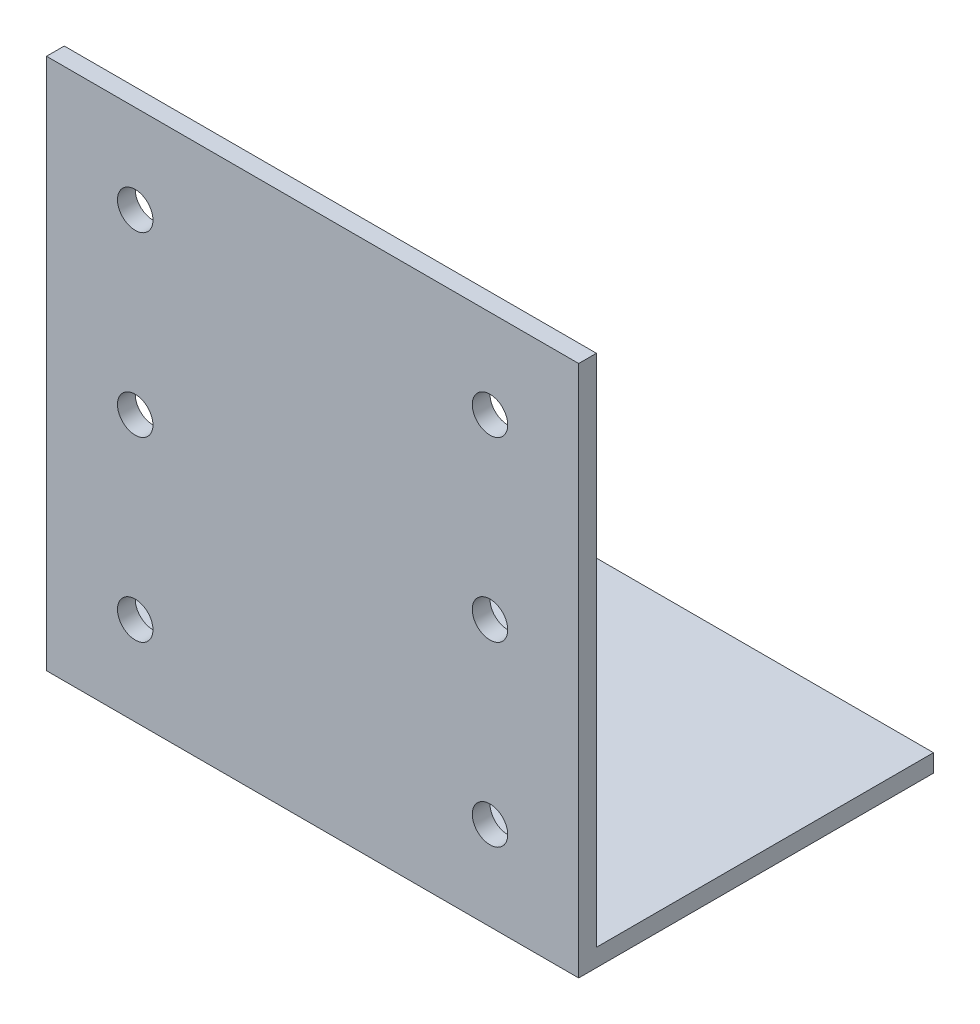
SolidWorks part; units mm, degrees
ref_plane "Спереди" through (0, 0, 0) normal (0, 0, 1) x (1, 0, 0)
ref_plane "Сверху" through (0, 0, 0) normal (0, 1, 0) x (1, 0, 0)
ref_plane "Справа" through (0, 0, 0) normal (1, 0, 0) x (0, 0, -1)
sketch "Эскиз1" plane through (0, 0, 0) normal (1, 0, 0) x (0, 0, -1)
  line L0 (0, 0) -> (0, 60)
  line L1 (0, 0) -> (40, 0)
extrude "Вытянуть-Тонкостенный1" add sketch "Эскиз1" along normal blind 60 thin
sketch "Эскиз2" plane through (0, 0, 0) normal (0, 0, 1) x (1, 0, 0)
  circle A0 centre (10, 50) radius 2
  circle A1 centre (50, 50) radius 2
  circle A2 centre (50, 30) radius 2
  circle A3 centre (50, 10) radius 2
  circle A5 centre (10, 30) radius 2
  circle A6 centre (10, 10) radius 2
  dimension "D1" = 2
  dimension "D2" = 3
extrude "Вырез-Вытянуть1" cut sketch "Эскиз2" against normal through all
